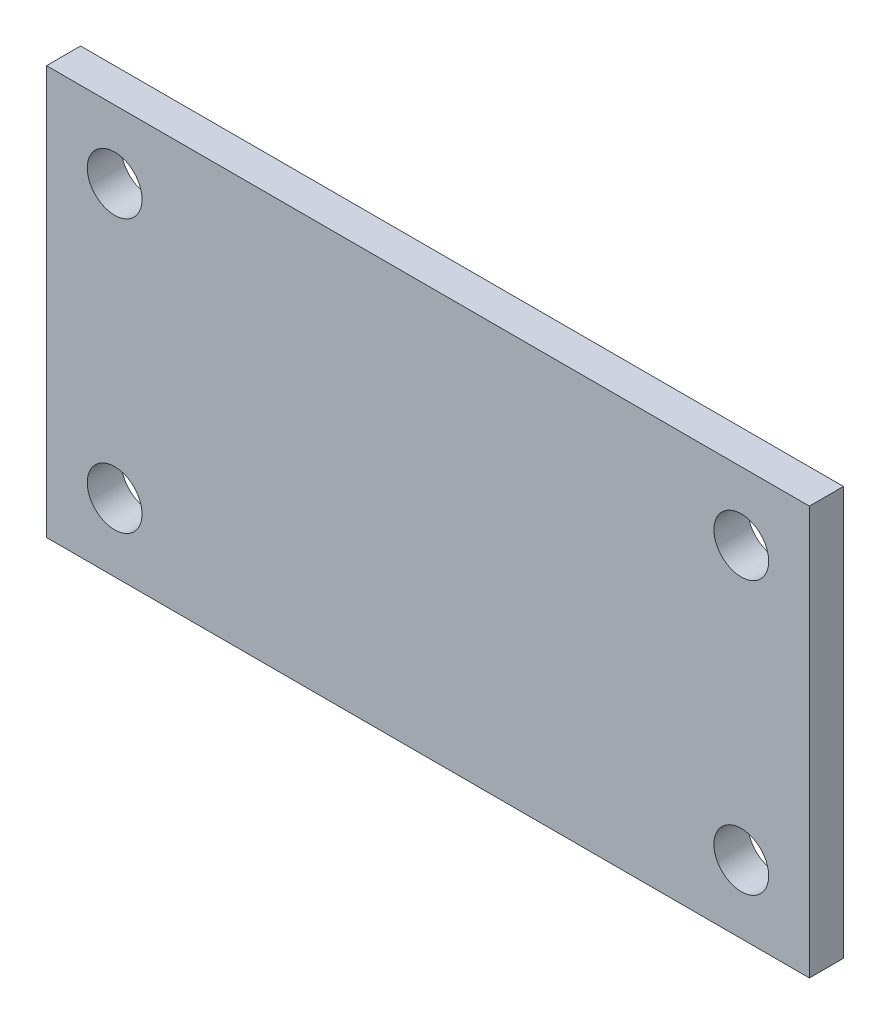
SolidWorks part; units mm, degrees
material "6063-T6"
ref_plane "Front" through (0, 0, 0) normal (0, 0, 1) x (1, 0, 0)
ref_plane "Top" through (0, 0, 0) normal (0, 1, 0) x (1, 0, 0)
ref_plane "Right" through (0, 0, 0) normal (1, 0, 0) x (0, 0, -1)
sketch "Sketch1" plane through (0, 0, 0) normal (0, 0, 1) x (1, 0, 0)
  line L1 (0, 0) -> (71.12, 0)
  line L2 (0, 0) -> (0, 38.1)
  line L3 (0, 38.1) -> (71.12, 38.1)
  line L4 (71.12, 0) -> (71.12, 38.1)
  line L5 (0, 0) -> (71.12, 38.1) construction
  line L6 (0, 38.1) -> (71.12, 0) construction
  point P4 (35.56, 19.05)
  dimension "D1" = 38.1
  dimension "D2" = 71.12
extrude "Boss-Extrude1" add sketch "Sketch1" along normal blind 3.175
sketch "Sketch2" plane through (0, 0, 0) normal (0, 0, -1) x (-1, 0, 0)
  line L0 (-6.35, 6.35) -> (0, 6.35) construction
  line L1 (0, 38.1) -> (0, 0) construction
  line L2 (-6.35, 6.35) -> (-6.35, 0) construction
  line L3 (0, 0) -> (-71.12, 0) construction
  line L4 (-35.56, 0) -> (-35.56, 11.9319) construction
  line L5 (0, 19.05) -> (-10.5889, 19.05) construction
  circle A0 centre (-6.35, 6.35) radius 2.5527
  circle A1 centre (-64.77, 6.35) radius 2.5527
  circle A2 centre (-64.77, 31.75) radius 2.5527
  circle A3 centre (-6.35, 31.75) radius 2.5527
  dimension "D1" = 6.35
extrude "Cut-Extrude1" cut sketch "Sketch2" against normal up to next
